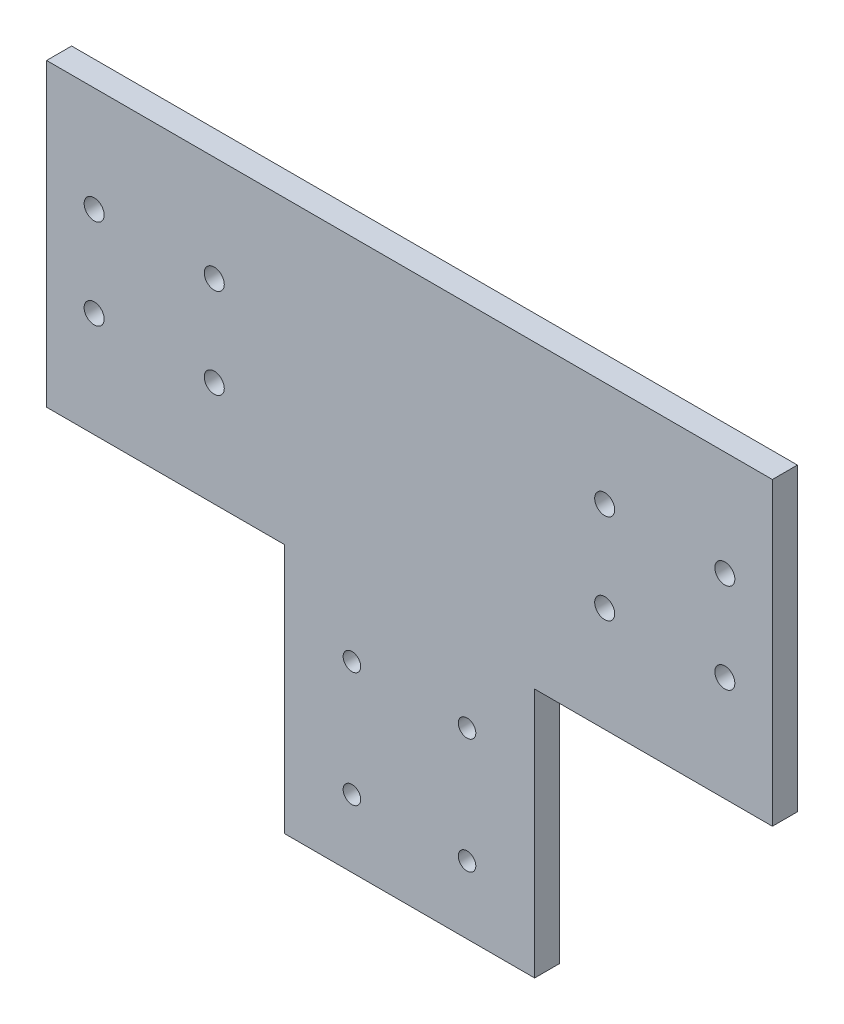
SolidWorks part; units mm, degrees
ref_plane "Front Plane" through (0, 0, 0) normal (0, 0, 1) x (1, 0, 0)
ref_plane "Top Plane" through (0, 0, 0) normal (0, 1, 0) x (1, 0, 0)
ref_plane "Right Plane" through (0, 0, 0) normal (1, 0, 0) x (0, 0, -1)
sketch "Sketch1" plane through (0, 0, 0) normal (0, 0, 1) x (1, 0, 0)
  line L0 (0, -55) -> (-25, -55) construction
  line L1 (-72.5, 30) -> (72.5, 30)
  line L2 (-72.5, 30) -> (-72.5, -30)
  line L3 (-72.5, -30) -> (-25, -30)
  line L4 (72.5, 30) -> (72.5, -30)
  line L5 (-72.5, 30) -> (72.5, -30) construction
  line L6 (-72.5, -30) -> (72.5, 30) construction
  line L8 (-25, -30) -> (-25, -80)
  line L9 (-25, -80) -> (25, -80)
  line L10 (25, -30) -> (25, -80)
  line L11 (-25, -30) -> (25, -80) construction
  line L12 (-25, -80) -> (25, -30) construction
  line L13 (0, 0) -> (0, 30) construction
  line L14 (25, -30) -> (72.5, -30)
  circle A0 centre (-11.5, -66.5) radius 1.75
  circle A1 centre (11.5, -66.5) radius 1.75
  circle A2 centre (11.5, -43.5) radius 1.75
  circle A3 centre (-11.5, -43.5) radius 1.75
  circle A4 centre (-63, 9) radius 2
  circle A5 centre (-39, 9) radius 2
  circle A6 centre (-39, -9) radius 2
  circle A7 centre (-63, -9) radius 2
  circle A8 centre (63, -9) radius 2
  circle A9 centre (39, -9) radius 2
  circle A10 centre (39, 9) radius 2
  circle A11 centre (63, 9) radius 2
  point P0 (0, 0)
  point P6 (0, -55)
  dimension "D5" = 11.5
  dimension "D1" = 145
  dimension "D2" = 60
  dimension "D3" = 50
  dimension "D4" = 50
extrude "Boss-Extrude1" add sketch "Sketch1" along normal blind 5
